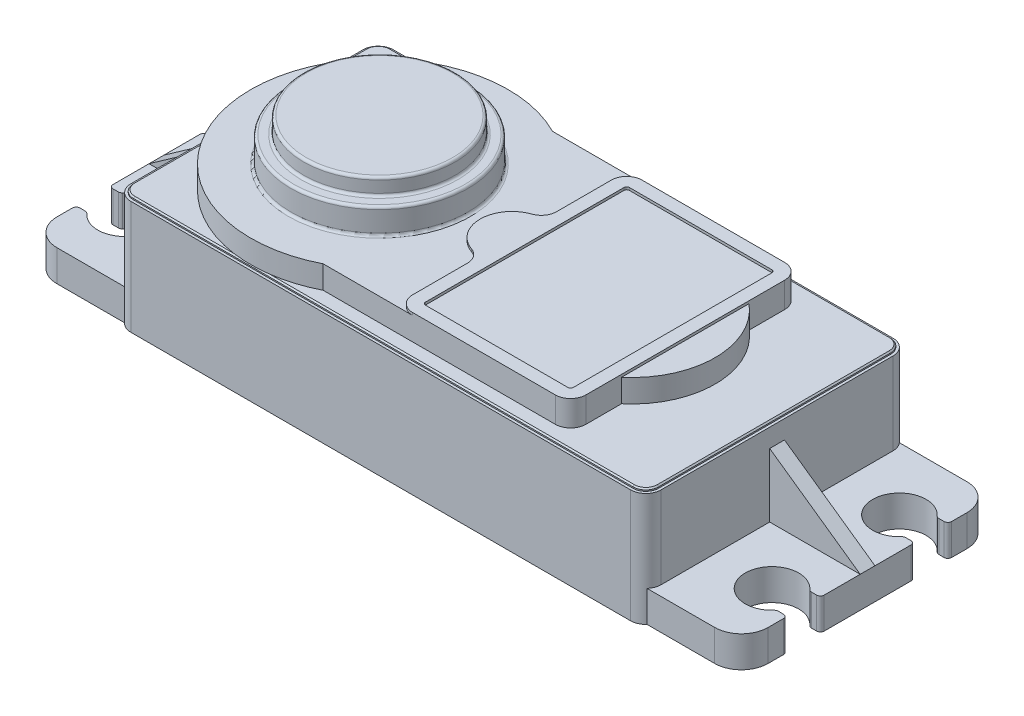
SolidWorks part; units mm, degrees
ref_plane "Alzado" through (0, 0, 0) normal (0, 0, 1) x (1, 0, 0)
ref_plane "Planta" through (0, 0, 0) normal (0, 1, 0) x (1, 0, 0)
ref_plane "Vista lateral" through (0, 0, 0) normal (1, 0, 0) x (0, 0, -1)
sketch "Croquis1" plane through (0, 0, 0) normal (0, 1, 0) x (1, 0, 0)
  line L1 (-20.8, -10.3) -> (20.8, -10.3)
  line L2 (-20.8, -10.3) -> (-20.8, 10.3)
  line L3 (-20.8, 10.3) -> (20.8, 10.3)
  line L4 (20.8, -10.3) -> (20.8, 10.3)
  line L5 (-20.8, -10.3) -> (20.8, 10.3) construction
  line L6 (-20.8, 10.3) -> (20.8, -10.3) construction
  point P0 (0, 0)
  dimension "D1" = 41.6
  dimension "D2" = 20.6
extrude "Saliente-Extruir1" add sketch "Croquis1" along normal blind 8.9
fillet "Redondeo1" radius 1.2 4 edges at (-20.8, 4.45, -10.3) (20.8, 4.45, -10.3) (20.8, 4.45, 10.3) (-20.8, 4.45, 10.3)
sketch "Croquis2" plane through (0, 0, 0) normal (0, -1, 0) x (1, 0, 0)
  line L0 (0, 0) -> (-20.8, 0) construction
  line L2 (-20.8, -9.1) -> (-20.8, 9.1) construction
  line L3 (-20.8, 0) -> (-28.0473, 0) construction
  line L4 (27.9, -9.9) -> (-27.9, -9.9)
  line L5 (27.9, -9.9) -> (27.9, 9.9)
  line L6 (27.9, 9.9) -> (-27.9, 9.9)
  line L7 (-27.9, -9.9) -> (-27.9, 9.9)
  line L8 (27.9, -9.9) -> (-27.9, 9.9) construction
  line L9 (27.9, 9.9) -> (-27.9, -9.9) construction
  dimension "D1" = 19.8
  dimension "D2" = 7.1
extrude "Saliente-Extruir2" add sketch "Croquis2" against normal blind 2.45
fillet "Redondeo2" radius 2.1 4 edges at (-27.9, 1.225, 9.9) (-27.9, 1.225, -9.9) (27.9, 1.225, -9.9) (27.9, 1.225, 9.9)
sketch "Croquis3" plane through (0, 0, 0) normal (0, -1, 0) x (1, 0, 0)
  line L0 (25.4, 9.9) -> (25.4, -9.9) construction
  line L1 (25.8, 9.9) -> (20.4944, 9.9) construction
  line L2 (20.4944, -9.9) -> (25.8, -9.9) construction
  line L3 (27.9, 0) -> (25.4, 0) construction
  line L4 (27.9, -7.8) -> (27.9, 7.8) construction
  line L5 (25.4, 5) -> (27.9, 5) construction
  line L6 (26.3441, -3.4416) -> (27.9, -6.3) construction
  line L7 (27.0492, 6.3) -> (27.9, 6.3)
  line L8 (26.3441, -6.5584) -> (27.9, -3.7) construction
  line L9 (27.0492, 3.7) -> (27.9, 3.7)
  line L10 (27.9, 6.3) -> (27.9, 3.7)
  line L11 (26.3441, 6.5584) -> (27.9, 3.7) construction
  line L12 (26.3441, 3.4416) -> (27.9, 6.3) construction
  line L13 (25.4, -5) -> (27.9, -5) construction
  line L14 (27.9, -6.3) -> (27.9, -3.7)
  line L15 (27.0492, -3.7) -> (27.9, -3.7)
  line L16 (27.0492, -6.3) -> (27.9, -6.3)
  line L17 (0, 0) -> (0, -10.3) construction
  line L18 (19.6, -10.3) -> (-19.6, -10.3) construction
  line L19 (-25.4, -5) -> (-27.9, -5) construction
  line L20 (-26.3441, 3.4416) -> (-27.9, 6.3) construction
  line L21 (-26.3441, 6.5584) -> (-27.9, 3.7) construction
  line L22 (-26.3441, -6.5584) -> (-27.9, -3.7) construction
  line L23 (-26.3441, -3.4416) -> (-27.9, -6.3) construction
  line L24 (-25.4, 5) -> (-27.9, 5) construction
  line L25 (-27.9, 0) -> (-25.4, 0) construction
  line L26 (-25.4, 9.9) -> (-25.4, -9.9) construction
  line L27 (-27.0492, -6.3) -> (-27.9, -6.3)
  line L28 (-27.0492, -3.7) -> (-27.9, -3.7)
  line L29 (-27.9, -6.3) -> (-27.9, -3.7)
  line L30 (-27.9, 6.3) -> (-27.9, 3.7)
  line L31 (-27.0492, 3.7) -> (-27.9, 3.7)
  line L32 (-27.0492, 6.3) -> (-27.9, 6.3)
  arc A0 (27.0492, 6.3) -> (27.0492, 3.7) centre (25.4, 5) ccw
  arc A1 (27.0492, -6.3) -> (27.0492, -3.7) centre (25.4, -5) cw
  arc A2 (-27.0492, -6.3) -> (-27.0492, -3.7) centre (-25.4, -5) ccw
  arc A3 (-27.0492, 6.3) -> (-27.0492, 3.7) centre (-25.4, 5) cw
  point P14 (27.1924, 5)
  point P27 (27.1924, -5)
  point P53 (-27.1924, -5)
  point P54 (-27.1924, 5)
  dimension "D1" = 4.2
  dimension "D3" = 2.5
  dimension "D4" = 2.6
extrude "Cortar-Extruir1" cut sketch "Croquis3" against normal blind 2.45
fillet "Redondeo3" radius 0.3 16 edges at (-27.9, 1.225, -3.7) (-27.0492, 1.225, -3.7) (-27.9, 1.225, -6.3) (-27.0492, 1.225, -6.3) (-27.9, 1.225, 3.7) (-27.0492, 1.225, 3.7) (-27.9, 1.225, 6.3) (-27.0492, 1.225, 6.3) (27.0492, 1.225, -3.7) (27.9, 1.225, -3.7) (27.9, 1.225, -6.3) (27.0492, 1.225, -6.3) (27.0492, 1.225, 6.3) (27.9, 1.225, 6.3) (27.9, 1.225, 3.7) (27.0492, 1.225, 3.7)
sketch "Croquis4" plane through (0, 8.9, 0) normal (0, 1, 0) x (1, 0, 0)
  line L24 (20.6, -9.1) -> (20.6, 9.1)
  line L25 (-19.6, -10.1) -> (19.6, -10.1)
  line L26 (-20.6, 9.1) -> (-20.6, -9.1)
  line L27 (19.6, 10.1) -> (-19.6, 10.1)
  line L28 (20.6, -9.1) -> (20.6, 9.1)
  line L29 (-19.6, -10.1) -> (19.6, -10.1)
  line L30 (-20.6, 9.1) -> (-20.6, -9.1)
  line L31 (19.6, 10.1) -> (-19.6, 10.1)
  arc A20 (20.6, 9.1) -> (19.6, 10.1) centre (19.6, 9.1) ccw
  arc A21 (19.6, -10.1) -> (20.6, -9.1) centre (19.6, -9.1) ccw
  arc A22 (-20.6, -9.1) -> (-19.6, -10.1) centre (-19.6, -9.1) ccw
  arc A23 (-19.6, 10.1) -> (-20.6, 9.1) centre (-19.6, 9.1) ccw
  arc A24 (20.6, 9.1) -> (19.6, 10.1) centre (19.6, 9.1) ccw
  arc A25 (19.6, -10.1) -> (20.6, -9.1) centre (19.6, -9.1) ccw
  arc A26 (-20.6, -9.1) -> (-19.6, -10.1) centre (-19.6, -9.1) ccw
  arc A27 (-19.6, 10.1) -> (-20.6, 9.1) centre (-19.6, 9.1) ccw
  dimension "D1" = 0.2
extrude "Saliente-Extruir3" add sketch "Croquis4" along normal blind 0.2
chamfer "Chaflán1" distance 0.1 angle 45 8 edges at (20.6, 9.1, 0) (20.3071, 9.1, 9.8071) (0, 9.1, 10.1) (-20.3071, 9.1, 9.8071) (-20.6, 9.1, 0) (-20.3071, 9.1, -9.8071) (0, 9.1, -10.1) (20.3071, 9.1, -9.8071)
sketch "Croquis6" plane through (0, 9.1, 0) normal (0, 1, 0) x (1, 0, 0)
  line L0 (0, 0) -> (-20.8, 0) construction
  line L1 (-20.8, -9.1) -> (-20.8, 9.1) construction
  line L2 (0, 0) -> (13.6, 0) construction
  line L4 (13.6, 0) -> (15.94, 0) construction
  line L5 (13.6, 5) -> (13.6, 9)
  line L6 (-20.6, 9.1) -> (-20.6, -9.1) construction
  line L7 (-5.8163, -9) -> (13.6, -9)
  line L9 (-5.8163, 9) -> (13.6, 9)
  line L10 (13.6, -9) -> (13.6, -5)
  line L11 (-13.6, -9) -> (13.6, 9) construction
  line L12 (-13.6, 9) -> (13.6, -9) construction
  arc A0 (13.6, -5) -> (13.6, 5) centre (9.4281, 0) ccw
  arc A1 (-5.8163, 9) -> (-5.8163, -9) centre (-10.4, 0) ccw
  dimension "D1" = 18
  dimension "D2" = 34.2
  dimension "D4" = 2.34
  dimension "D3" = 10
extrude "Saliente-Extruir4" add sketch "Croquis6" along normal blind 1.8
fillet "Redondeo5" radius 1.2 2 edges at (13.6, 10, -9) (13.6, 10, 9)
sketch "Croquis10" plane through (0, 10.9, 0) normal (0, 1, 0) x (1, 0, 0)
  line L0 (13.6, 7.8) -> (13.6, -7.8)
  line L1 (0, 7.8) -> (0, 3.5)
  line L2 (12.4, 9) -> (-5.8163, 9) construction
  line L3 (-5.8163, -9) -> (12.4, -9) construction
  line L4 (1.2, -9) -> (12.4, -9)
  line L5 (12.4, 9) -> (1.2, 9)
  line L6 (0, -3.5) -> (0, -7.8)
  line L7 (6.8, 9) -> (6.8, -9) construction
  line L8 (12.4, 8) -> (1.2, 8)
  line L9 (1.2, -8) -> (12.4, -8)
  line L10 (1, -7.8) -> (1, 7.8)
  line L11 (12.6, 7.8) -> (12.6, -7.8)
  arc A0 (13.6, 7.8) -> (12.4, 9) centre (12.4, 7.8) ccw construction
  arc A1 (12.4, -9) -> (13.6, -7.8) centre (12.4, -7.8) ccw construction
  arc A2 (13.6, 7.8) -> (12.4, 9) centre (12.4, 7.8) ccw
  arc A3 (12.4, -9) -> (13.6, -7.8) centre (12.4, -7.8) ccw
  arc A4 (0, -7.8) -> (1.2, -9) centre (1.2, -7.8) ccw
  arc A5 (0, 7.8) -> (1.2, 9) centre (1.2, 7.8) cw
  arc A6 (-0.8108, 2.3649) -> (-0.8108, -2.3649) centre (0, 0) ccw
  arc A7 (-0.8108, -2.3649) -> (0, -3.5) centre (-1.2, -3.5) cw
  arc A8 (-0.8108, 2.3649) -> (0, 3.5) centre (-1.2, 3.5) ccw
  arc A9 (12.6, 7.8) -> (12.4, 8) centre (12.4, 7.8) ccw
  arc A10 (1, 7.8) -> (1.2, 8) centre (1.2, 7.8) cw
  arc A11 (1, -7.8) -> (1.2, -8) centre (1.2, -7.8) ccw
  arc A12 (12.4, -8) -> (12.6, -7.8) centre (12.4, -7.8) ccw
  point P15 (0, -9)
  point P18 (0, 9)
  point P24 (0, -2.5)
  dimension "D1" = 1.2
  dimension "D2" = 1.2
  dimension "D3" = 1
extrude "Saliente-Extruir5" add sketch "Croquis10" along normal blind 0.2
sketch "Croquis11" plane through (0, 10.9, 0) normal (0, 1, 0) x (1, 0, 0)
  circle A0 centre (-10.4, 0) radius 6.95
  dimension "D1" = 13.9
extrude "Saliente-Extruir6" add sketch "Croquis11" along normal blind 2
fillet "Redondeo6" radius 0.2 2 edges at (-10.4, 10.9, 6.95) (-10.4, 12.9, 6.95)
sketch "Croquis12" plane through (0, 12.9, 0) normal (0, 1, 0) x (1, 0, 0)
  circle A0 centre (-10.4, 0) radius 5.95
  dimension "D1" = 11.9
extrude "Saliente-Extruir7" add sketch "Croquis12" along normal blind 1.3
fillet "Redondeo7" radius 0.2 2 edges at (-10.4, 12.9, 5.95) (-10.4, 14.2, 5.95)
ref_plane "Plano1" through (0, 0, 0) normal (0, 0, 1) x (1, 0, 0)
sketch "Croquis13" plane through (0, 0, 0) normal (0, 0, 1) x (1, 0, 0)
  line L0 (20.8, 2.45) -> (27.9, 2.45)
  line L1 (25.8, 2.45) -> (20.4944, 2.45) construction
  line L2 (20.8, 8.9) -> (20.8, 2.45) construction
  line L3 (27.9, 2.45) -> (20.8, 7.45)
  line L4 (20.8, 7.45) -> (20.8, 2.45)
  line L5 (-27.9, 2.45) -> (-20.8, 2.45)
  line L6 (-20.8, 2.45) -> (-20.8, 7.45)
  line L7 (-20.8, 2.45) -> (-20.8, 8.9) construction
  line L8 (-20.8, 7.45) -> (-27.9, 2.45)
  dimension "D1" = 5
extrude "Saliente-Extruir8" add sketch "Croquis13" along normal mid plane 1.16
